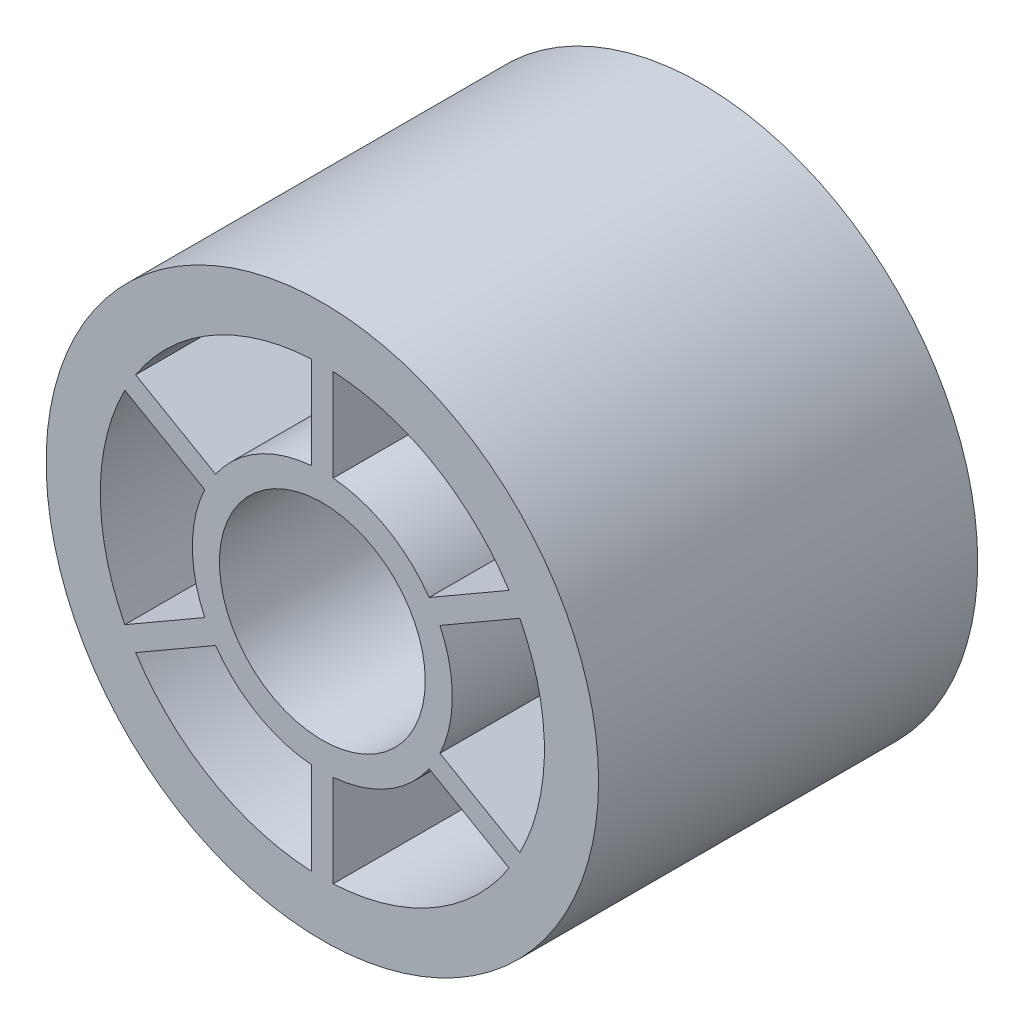
SolidWorks part; units mm, degrees
ref_plane "Plan de face" through (0, 0, 0) normal (0, 0, 1) x (1, 0, 0)
ref_plane "Plan de dessus" through (0, 0, 0) normal (0, 1, 0) x (1, 0, 0)
ref_plane "Plan de droite" through (0, 0, 0) normal (1, 0, 0) x (0, 0, -1)
sketch "Esquisse1" plane through (0, 0, 0) normal (0, 0, 1) x (1, 0, 0)
  line L0 (10.8562, 5.1131) -> (18.2324, 9.3718)
  line L1 (9.8562, 6.8452) -> (17.2324, 11.1038)
  line L2 (9.8562, -6.8452) -> (17.2324, -11.1038)
  line L3 (1, 11.9583) -> (1, 20.4756)
  line L4 (10.8562, -5.1131) -> (18.2324, -9.3718)
  line L5 (-1, 11.9583) -> (-1, 20.4756)
  line L6 (-1, -11.9583) -> (-1, -20.4756)
  line L7 (1, -11.9583) -> (1, -20.4756)
  line L8 (-10.8562, -5.1131) -> (-18.2324, -9.3718)
  line L9 (-9.8562, -6.8452) -> (-17.2324, -11.1038)
  line L10 (-9.8562, 6.8452) -> (-17.2324, 11.1038)
  line L11 (-10.8562, 5.1131) -> (-18.2324, 9.3718)
  arc A0 (9.8562, 6.8452) -> (1, 11.9583) centre (0, 0) ccw
  circle A1 centre (0, 0) radius 25.5
  arc A2 (-1, 20.4756) -> (-17.2324, 11.1038) centre (0, 0) ccw
  arc A3 (-1, 11.9583) -> (-9.8562, 6.8452) centre (0, 0) ccw
  arc A4 (17.2324, 11.1038) -> (1, 20.4756) centre (0, 0) ccw
  arc A5 (18.2324, -9.3718) -> (18.2324, 9.3718) centre (0, 0) ccw
  arc A6 (10.8562, -5.1131) -> (10.8562, 5.1131) centre (0, 0) ccw
  arc A7 (1, -11.9583) -> (9.8562, -6.8452) centre (0, 0) ccw
  arc A8 (1, -20.4756) -> (17.2324, -11.1038) centre (0, 0) ccw
  arc A9 (-17.2324, -11.1038) -> (-1, -20.4756) centre (0, 0) ccw
  arc A10 (-9.8562, -6.8452) -> (-1, -11.9583) centre (0, 0) ccw
  arc A11 (-10.8562, 5.1131) -> (-10.8562, -5.1131) centre (0, 0) ccw
  arc A12 (-18.2324, 9.3718) -> (-18.2324, -9.3718) centre (0, 0) ccw
  circle A13 centre (0, 0) radius 9.5
extrude "Extrusion1" add sketch "Esquisse1" along normal blind 35
